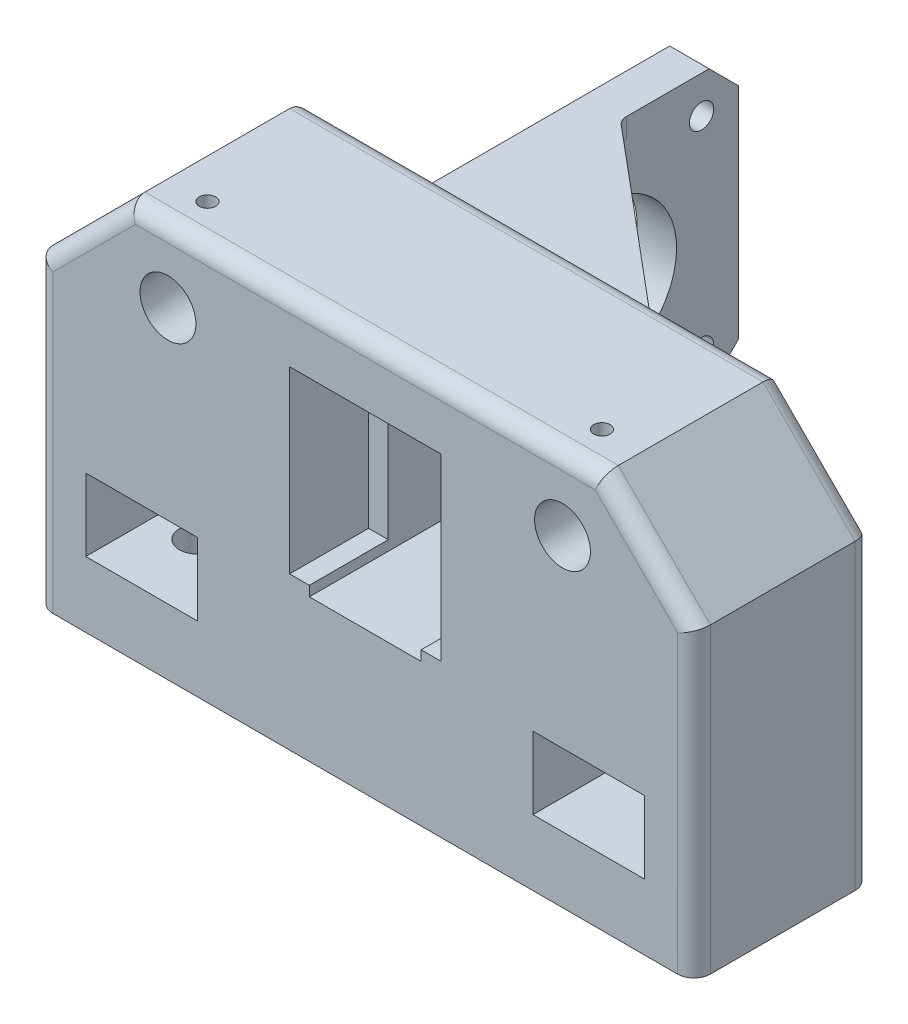
SolidWorks part; units mm, degrees
ref_plane "Front Plane" through (0, 0, 0) normal (0, 0, 1) x (1, 0, 0)
ref_plane "Top Plane" through (0, 0, 0) normal (0, 1, 0) x (1, 0, 0)
ref_plane "Right Plane" through (0, 0, 0) normal (1, 0, 0) x (0, 0, -1)
sketch "Sketch1" plane through (0, 0, 0) normal (0, 0, 1) x (1, 0, 0)
  line L0 (0, 0) -> (0, -10) construction
  line L1 (-50, 11) -> (50, 11)
  line L9 (-50, 11) -> (-50, -49)
  line L10 (-50, -49) -> (50, -49)
  line L11 (50, 11) -> (50, -49)
  circle A0 centre (30, 0) radius 4.25
  circle A1 centre (-30, 0) radius 4.25
  point P0 (0, 0)
  dimension "D3" = 60
  dimension "D4" = 8.5
  dimension "D6" = 11
  dimension "D1" = 100
  dimension "D2" = 60
extrude "Boss-Extrude1" add sketch "Sketch1" along normal mid plane 27
sketch "Sketch2" plane through (0, 0, -13.5) normal (0, 0, -1) x (-1, 0, 0)
  circle A0 centre (-30, 0) radius 7
  circle A1 centre (30, 0) radius 7
  dimension "D1" = 14
extrude "Boss-Extrude2" add sketch "Sketch2" against normal blind 10
chamfer "Chamfer1" distance 14 angle 45 2 edges at (-50, 11, 0) (50, 11, 0)
fillet "Fillet1" radius 2.5 10 edges at (50, -26, 13.5) (43, 4, 13.5) (-43, 4, 13.5) (0, 11, 13.5) (-50, -26, 13.5) (-50, -26, -13.5) (-43, 4, -13.5) (0, 11, -13.5) (43, 4, -13.5) (50, -26, -13.5)
sketch "Sketch3" plane through (0, 0, 13.5) normal (0, 0, 1) x (1, 0, 0)
  line L0 (-36, 11) -> (36, 11) construction
  line L1 (11.5, 1.5) -> (-11.5, 1.5)
  line L3 (11.5, -25.79) -> (-11.5, -25.79)
  line L4 (-11.5, 1.5) -> (-11.5, -14.75)
  line L5 (11.5, 1.5) -> (-11.5, -25.79) construction
  line L6 (11.5, -25.79) -> (-11.5, 1.5) construction
  line L7 (-47.5, -49) -> (47.5, -49) construction
  line L8 (0, 0) -> (0, -65.5698) construction
  line L9 (11.5, 1.5) -> (11.5, -14.75)
  line L14 (11.5, -14.75) -> (11.5, -25.79)
  line L26 (-11.5, -14.75) -> (-11.5, -25.79)
  point P0 (0, -12.145)
  dimension "D2" = 9.5
  dimension "D3" = 23.21
  dimension "D5" = 23
extrude "Cut-Extrude1" cut sketch "Sketch3" against normal blind 12 contours L3 L26 L4 L1 L9 L14
sketch "Sketch5" plane through (0, 11, 0) normal (0, 1, 0) x (1, 0, 0)
  line L0 (30, -7.5) -> (30, 3.5) construction
  line L1 (25.75, 3.5) -> (34.25, 3.5) construction
  line L2 (34.9645, -13.5) -> (-34.9645, -13.5) construction
  line L3 (0, 0) -> (0, 27.1872) construction
  line L4 (-30, -7.5) -> (-30, 3.5) construction
  circle A0 centre (30, -7.5) radius 1.25
  circle A1 centre (-30, -7.5) radius 1.25
  dimension "D1" = 2.5
  dimension "D2" = 6
extrude "Cut-Extrude2" cut sketch "Sketch5" against normal blind 12
sketch "Sketch6" plane through (0, -49, 0) normal (0, -1, 0) x (1, 0, 0)
  line L0 (-47.5, 13.5) -> (47.5, 13.5) construction
  circle A0 centre (36.2778, 2.75) radius 2.75
  dimension "D1" = 5.5
  dimension "D2" = 8
extrude "Cut-Extrude3" cut sketch "Sketch6" against normal blind 10
sketch "Sketch7" plane through (0, 0, 13.5) normal (0, 0, 1) x (1, 0, 0)
  line L0 (36.5278, -41.042) -> (36.5278, -50.724) construction
  line L1 (42.5, -39) -> (30.5, -39)
  line L2 (42.5, -39) -> (42.5, -28)
  line L3 (42.5, -28) -> (30.5, -28)
  line L5 (39.0278, -49) -> (39.0278, -39) construction
  line L6 (50, -3) -> (50, -49) construction
  line L7 (30.5, -28) -> (25.5, -28)
  line L9 (30.5, -39) -> (25.5, -39)
  line L10 (25.5, -28) -> (25.5, -39)
  dimension "D1" = 11
  dimension "D2" = 2.5
  dimension "D3" = 12
  dimension "D4" = 7.5
  dimension "D5" = 17
extrude "Cut-Extrude4" cut sketch "Sketch7" against normal blind 17 contours L2 L3 L7 L10 L9 L1
mirror "Mirror1" about plane through (0, 0, 0) normal (1, 0, 0) of "Cut-Extrude4", "Cut-Extrude3"
ref_plane "Plane1" through (-18.5, 0, 0) normal (1, 0, 0) x (0, 0, -1)
sketch "Sketch11" plane through (0, 0, -13.5) normal (0, 0, -1) x (-1, 0, 0)
  line L0 (-7.92, -1.8052) -> (7.08, -1.8052) construction
  line L1 (-8.5, -27.3152) -> (8.5, -27.3152)
  line L2 (-8.5, -27.3152) -> (-8.5, 0.6948)
  line L3 (-8.5, 0.6948) -> (8.5, 0.6948)
  line L4 (8.5, -27.3152) -> (8.5, 0.6948)
  line L5 (-8.5, -27.3152) -> (8.5, 0.6948) construction
  line L6 (-8.5, 0.6948) -> (8.5, -27.3152) construction
  line L9 (-7.92, -24.8152) -> (7.08, -24.8152) construction
  point P0 (0, -13.3102)
  dimension "D1" = 2.5
  dimension "D2" = 2.5
  dimension "D3" = 17
extrude "Cut-Extrude5" cut sketch "Sketch11" against normal through all
sketch "Sketch13" plane through (0, 0, -3.5) normal (0, 0, 1) x (1, 0, 0)
  circle A1 centre (30, 0) radius 4.25
  circle A2 centre (30, 0) radius 4.25
  circle A3 centre (-30, 0) radius 4.25
  circle A4 centre (-30, 0) radius 4.25
  dimension "D1" = 0
  dimension "D2" = 0
extrude "Boss-Extrude6" add sketch "Sketch13" along normal blind 9
sketch "Sketch14" plane through (-18.5, 0, 0) normal (1, 0, 0) x (0, 0, -1)
  line L0 (55.8, -29.9602) -> (55.8, 3.3398) construction
  line L1 (55.8, -29.9602) -> (55.8, 3.3398)
  line L2 (55.8, 3.3398) -> (51.3, 7.8398) construction
  line L3 (51.3, 7.8398) -> (18, 7.8398) construction
  line L4 (18, -34.4602) -> (51.3, -34.4602) construction
  line L5 (51.3, -34.4602) -> (55.8, -29.9602) construction
  line L6 (55.8, 3.3398) -> (51.3, 7.8398)
  line L7 (51.3, 7.8398) -> (18, 7.8398)
  line L8 (18, -34.4602) -> (51.3, -34.4602)
  line L9 (51.3, -34.4602) -> (55.8, -29.9602)
  line L10 (18, -34.4602) -> (11, -34.4602)
  line L11 (11, -49) -> (11, -3) construction
  line L12 (11, -34.4602) -> (11, 7.8398)
  line L13 (11, -3) -> (11, 11) construction
  line L14 (11, 7.8398) -> (18, 7.8398)
  circle A0 centre (50.15, -28.8102) radius 1.85
  circle A1 centre (50.15, 2.1898) radius 1.85
  circle A2 centre (19.15, 2.1898) radius 1.85
  circle A3 centre (19.15, -28.8102) radius 1.85
  circle A4 centre (34.65, -13.3102) radius 11.7
  dimension "D1" = 3.7
  dimension "D2" = 23.4
extrude "Boss-Extrude7" add sketch "Sketch14" along normal blind 6
sketch "Sketch15" plane through (0, -34.4602, 0) normal (0, -1, 0) x (1, 0, 0)
  line L0 (-14.5, -39.5) -> (20.0609, -10.5)
  line L1 (20.0609, -10.5) -> (-14.5, -10.5)
  line L4 (-14.5, -10.5) -> (-14.5, -39.5)
  line L5 (-47.5, -13.5) -> (47.5, -13.5) construction
  line L6 (-12.5, -13.5) -> (-12.5, -51.3) construction
  dimension "D1" = 3
  dimension "D2" = 2
  dimension "D3" = 26
  dimension "D4" = 40
extrude "Boss-Extrude8" add sketch "Sketch15" against normal blind 3 from offset 4
ref_plane "Plane2" through (0, -13.3102, 0) normal (0, -1, 0) x (-1, 0, 0)
sketch "Sketch17" plane through (0, -34.4602, 0) normal (0, -1, 0) x (1, 0, 0)
  line L1 (-12.5, -51.3) -> (-18.5, -51.3)
  line L2 (-12.5, -51.3) -> (-12.5, -8.5813)
  line L3 (-12.5, -8.5813) -> (-18.5, -8.5813)
  line L4 (-18.5, -51.3) -> (-18.5, -8.5813)
  line L6 (-18.5, -13.5) -> (-18.5, -51.3) construction
extrude "Boss-Extrude9" add sketch "Sketch17" along normal blind 1
sketch "Sketch18" plane through (0, -35.4602, 0) normal (0, -1, 0) x (1, 0, 0)
  line L0 (-18.5, -13.5) -> (-18.5, -51.3) construction
  line L3 (-18.5, -10.5) -> (-41.5752, -10.5)
  line L5 (-18.5, -38) -> (-41.5752, -10.5)
  line L6 (-18.5, -38) -> (-11.2231, -38) construction
  line L7 (-47.5, -13.5) -> (47.5, -13.5) construction
  line L9 (-18.5, -38) -> (-13.7392, -38)
  line L11 (-18.5, -10.5) -> (-13.7392, -10.5)
  line L12 (-13.7392, -38) -> (-13.7392, -10.5)
  dimension "D1" = 24.5
  dimension "D2" = 3
  dimension "D3" = 50
  dimension "D4" = 4.7608
extrude "Boss-Extrude12" add sketch "Sketch18" along normal blind 3
sketch "Sketch19" plane through (0, -38.4602, 0) normal (0, -1, 0) x (1, 0, 0)
  line L0 (-39.0579, -13.5) -> (16.4856, -13.5) construction
  line L1 (-12.5, -38) -> (-18.5, -38)
  line L2 (-12.5, -38) -> (-12.5, -13.5)
  line L3 (-12.5, -13.5) -> (-18.5, -13.5)
  line L4 (-18.5, -38) -> (-18.5, -13.5)
  line L5 (-18.5, -38) -> (-18.5, -51.3) construction
  line L6 (-18.5, -38) -> (-14.5, -38) construction
extrude "Boss-Extrude13" add sketch "Sketch19" against normal blind 6
sketch "Sketch21" plane through (0, -35.4602, 0) normal (0, -1, 0) x (1, 0, 0)
  line L0 (-18.5, -51.3) -> (-18.5, -55.8) construction
  line L1 (-12.5, -51.3) -> (-18.5, -51.3)
  line L2 (-12.5, -51.3) -> (-12.5, -30.0188)
  line L3 (-12.5, -30.0188) -> (-18.5, -30.0188)
  line L4 (-18.5, -51.3) -> (-18.5, -30.0188)
extrude "Boss-Extrude14" add sketch "Sketch21" along normal up to surface (3 mm away) up to face at (-13.4731, -38.4602, -32.0402)
sketch "Sketch22" plane through (0, 7.8398, 0) normal (0, 1, 0) x (1, 0, 0)
  line L0 (36, 11) -> (-36, 11) construction
  line L1 (-12.5, 37.8218) -> (-15.5, 37.8218)
  line L3 (-12.5, 37.8218) -> (-12.5, 13.5)
  line L4 (-12.5, 13.5) -> (16.4856, 13.5)
  line L5 (16.4856, 13.5) -> (-12.5, 37.8218)
  line L8 (16.4856, 13.5) -> (-12.5, 37.8218)
  line L9 (-12.5, 11) -> (-15.5, 11)
  line L10 (-15.5, 37.8218) -> (-15.5, 11)
  line L14 (-12.5, 11) -> (16.4856, 11)
  line L15 (16.4856, 13.5) -> (16.4856, 11)
  dimension "D2" = 3
  dimension "D1" = 0
extrude "Boss-Extrude15" add sketch "Sketch22" against normal blind 3
fillet "Fillet3" radius 2 11 edges at (-12.5, 6.3398, -37.8218) (-39.0579, -36.9602, -13.5) (-18.5, -36.9602, -38) (16.4856, 6.3398, -13.5) (16.4856, -36.9602, -13.5) (-12.5, -36.9602, -37.8218) (-11.2862, -38.4602, -13.5) (-12.5, -35.4602, -25.6609) (1.9928, -35.4602, -13.5) (-12.5, -15.3102, -13.5) (1.9928, 4.8398, -13.5)
